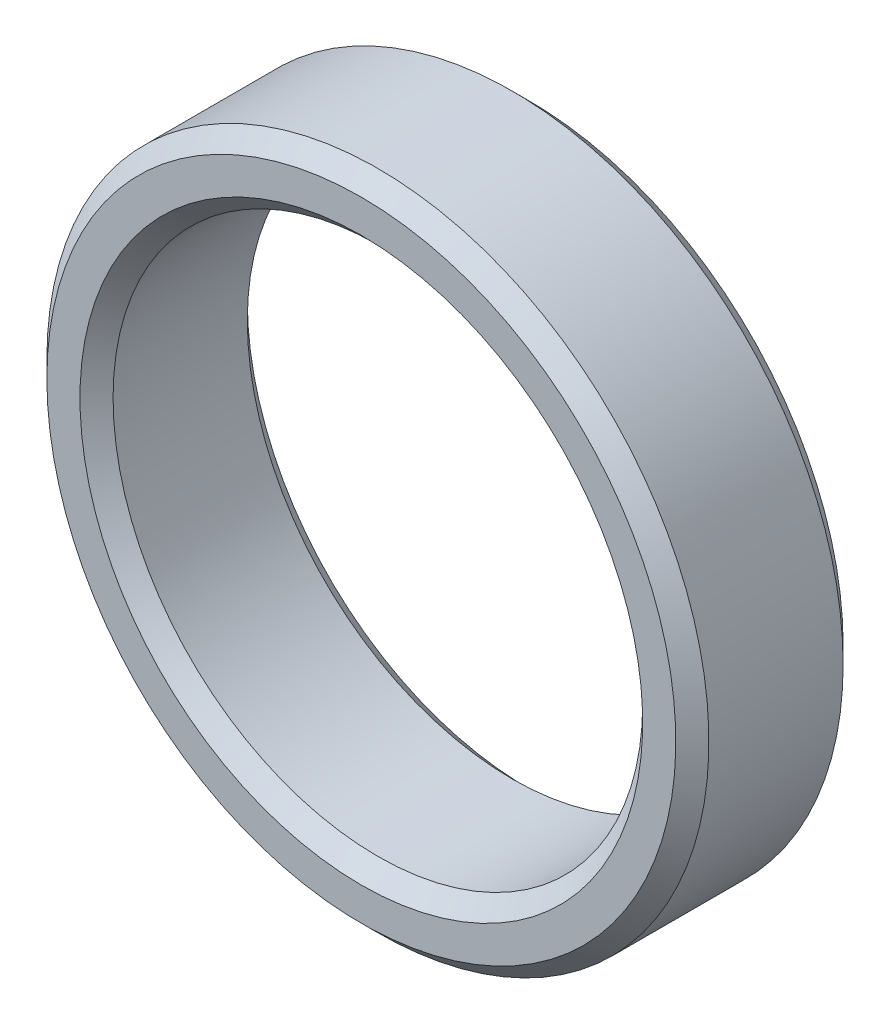
SolidWorks part; units mm, degrees
material "6061-T6 (SS)"
ref_plane "Front" through (0, 0, 0) normal (0, 0, 1) x (1, 0, 0)
ref_plane "Top" through (0, 0, 0) normal (0, 1, 0) x (1, 0, 0)
ref_plane "Right" through (0, 0, 0) normal (1, 0, 0) x (0, 0, -1)
sketch "Sketch1" plane through (0, 0, 0) normal (0, 0, 1) x (1, 0, 0)
  circle A0 centre (0, 0) radius 12.7
  circle A1 centre (0, 0) radius 15.875
  dimension "D1" = 25.4
  dimension "D2" = 31.75
extrude "Boss-Extrude1" add sketch "Sketch1" along normal up to surface (8.025 mm away)
chamfer "Chamfer1" distance 0.7937 angle 45 4 edges at (12.7, 0, 0) (15.875, 0, 0) (0, 15.875, 8.025) (0, 12.7, 8.025)
